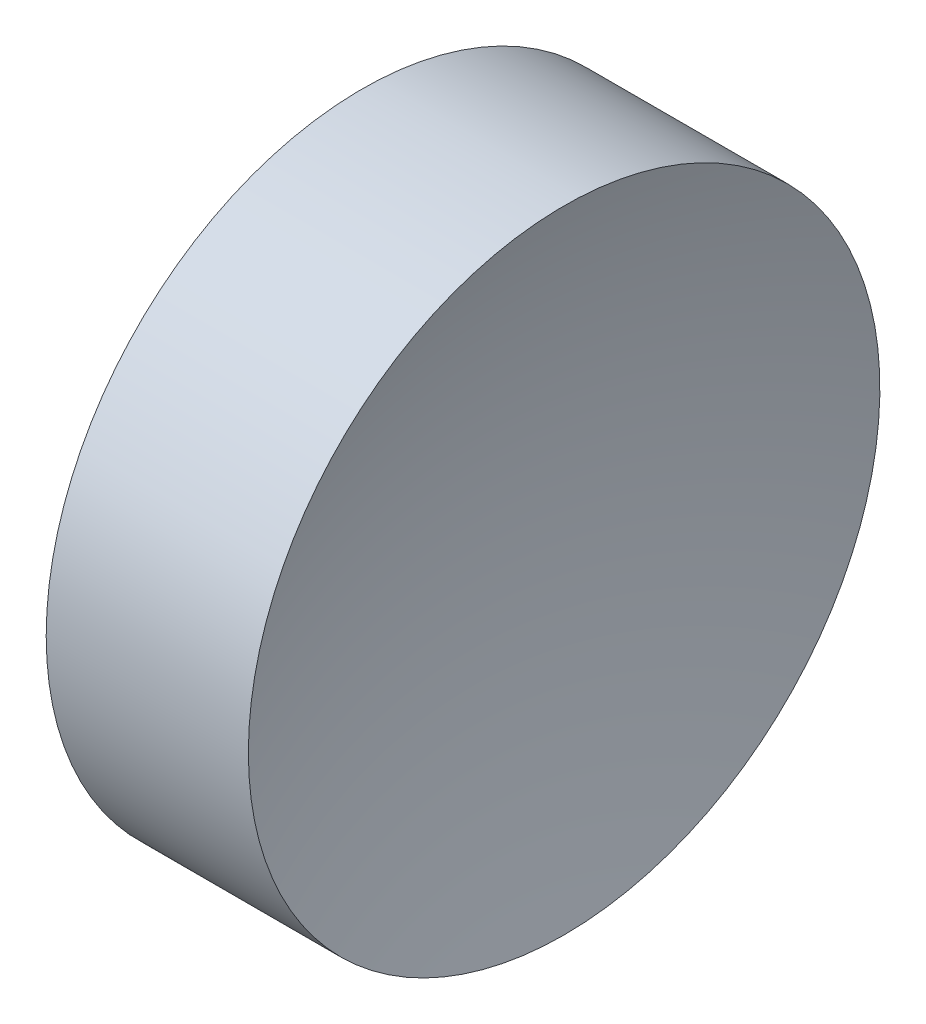
SolidWorks part; units mm, degrees
ref_plane "前视基准面" through (0, 0, 0) normal (0, 0, 1) x (1, 0, 0)
ref_plane "上视基准面" through (0, 0, 0) normal (0, 1, 0) x (1, 0, 0)
ref_plane "右视基准面" through (0, 0, 0) normal (1, 0, 0) x (0, 0, -1)
sketch "草图1" plane through (0, 0, 0) normal (0, 0, 1) x (1, 0, 0)
  line L0 (54.4926, 34.689) -> (66.3882, 34.689) construction
  line L1 (57.5463, 34.689) -> (57.5463, 40.939)
  line L2 (57.5463, 40.939) -> (61.548, 40.939)
  line L3 (60.5463, 34.689) -> (57.5463, 34.689)
  arc A0 (61.548, 40.939) -> (60.5463, 34.689) centre (80.5463, 34.689) ccw
  dimension "D1" = 4.0016
  dimension "D2" = 6.25
revolve "旋转1" add sketch "草图1" angle 360 about L0
